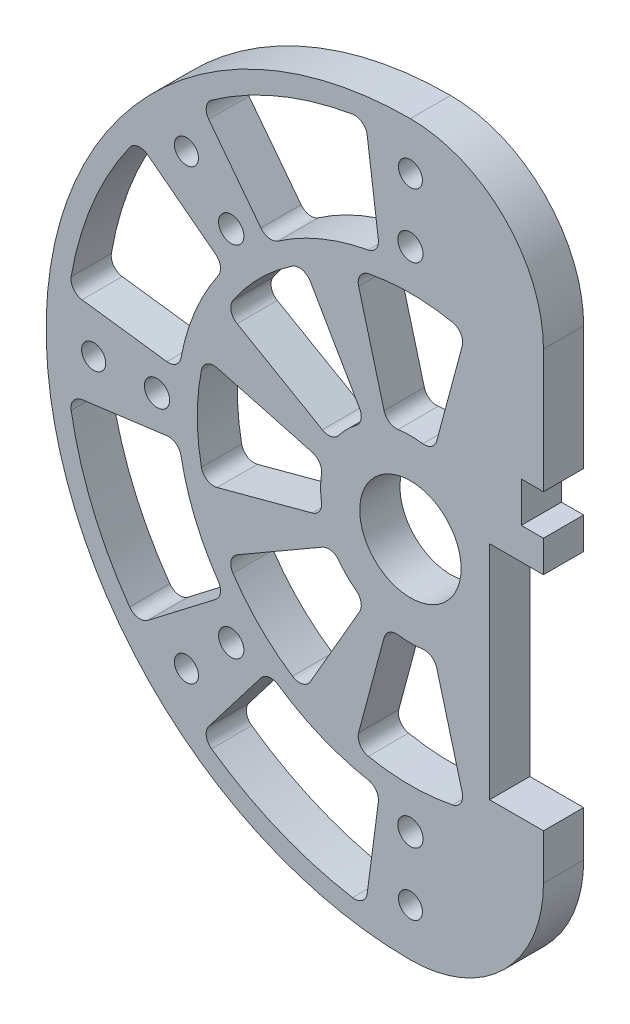
SolidWorks part; units mm, degrees
material "Balsa"
ref_plane "Front Plane" through (0, 0, 0) normal (0, 0, 1) x (1, 0, 0)
ref_plane "Top Plane" through (0, 0, 0) normal (0, 1, 0) x (1, 0, 0)
ref_plane "Right Plane" through (0, 0, 0) normal (1, 0, 0) x (0, 0, -1)
sketch "Sketch1" plane through (0, 0, 0) normal (0, 0, 1) x (1, 0, 0)
  line L0 (45.3154, 21.1309) -> (0, 0) construction
  line L1 (0, 0) -> (35.3553, -35.3553) construction
  line L2 (49.9788, 1.4542) -> (0, 0) construction
  line L3 (0, 0) -> (46.4674, -18.4603) construction
  circle A0 centre (45.3154, 21.1309) radius 1.8986
  circle A1 centre (46.4674, -18.4603) radius 1.9939
  circle A2 centre (0, 0) radius 57.5
  circle A3 centre (0, 0) radius 8
  circle A4 centre (49.9788, 1.4542) radius 1.9939
  circle A5 centre (0, 0) radius 40 construction
  circle A6 centre (0, 0) radius 50 construction
  circle A29 centre (0, -40) radius 1.9939
  circle A30 centre (0, -50) radius 1.8986
  circle A37 centre (-28.2843, -28.2843) radius 1.9939
  circle A38 centre (-35.3553, -35.3553) radius 1.8986
  circle A39 centre (-40, 0) radius 1.9939
  circle A40 centre (-50, 0) radius 1.8986
  circle A41 centre (-28.2843, 28.2843) radius 1.9939
  circle A42 centre (-35.3553, 35.3553) radius 1.8986
  circle A43 centre (0, 40) radius 1.9939
  circle A44 centre (0, 50) radius 1.8986
  circle A45 centre (28.2843, 28.2843) radius 1.9939 construction
  circle A46 centre (35.3553, 35.3553) radius 1.8986 construction
  circle A47 centre (40, 0) radius 1.9939 construction
  circle A48 centre (50, 0) radius 1.8986 construction
  circle A49 centre (28.2843, -28.2843) radius 1.9939 construction
  circle A50 centre (35.3553, -35.3553) radius 1.8986
  dimension "D1" = 115
  dimension "D4" = 3.7973
  dimension "D6" = 100
  dimension "D7" = 80
  dimension "D8" = 3.9878
  dimension "D9" = 3.9878
  dimension "D10" = 23.333
  dimension "D15" = 3.7973
  dimension "D16" = 3.9878
  dimension "D5" = 70
  dimension "D3" = 16
  dimension "D11" = 23.333
  dimension "D21" = 8
extrude "Boss-Extrude1" add sketch "Sketch1" along normal blind 6.35
sketch "Sketch2" plane through (0, 0, 0) normal (0, 0, 1) x (1, 0, 0)
  line L0 (12.5, -29.35) -> (41, -29.35)
  line L1 (41, -29.35) -> (41, 10.65)
  line L2 (41, 10.65) -> (44.5, 10.65)
  line L3 (44.5, 10.65) -> (44.5, 17)
  line L4 (44.5, 17) -> (41, 17)
  line L5 (41, 17) -> (41, 32)
  line L6 (41, 32) -> (21, 32)
  line L7 (21, 32) -> (21, 17)
  line L8 (21, 17) -> (17.5, 17)
  line L9 (17.5, 17) -> (17.5, 10.65)
  line L10 (17.5, 10.65) -> (21, 10.65)
  line L11 (21, 10.65) -> (21, 5.65)
  line L12 (21, 5.65) -> (12.5, 5.65)
  line L13 (12.5, 5.65) -> (12.5, -29.35)
  dimension "D2" = 20
  dimension "D3" = 3.5
  dimension "D4" = 3.5
  dimension "D5" = 15
  dimension "D6" = 21
  dimension "D7" = 6.35
  dimension "D8" = 5
  dimension "D9" = 40
  dimension "D10" = 8.5
  dimension "D11" = 32
extrude "Cut-Extrude1" cut sketch "Sketch2" along normal through all
sketch "Sketch3" plane through (0, 0, 6.35) normal (0, 0, 1) x (1, 0, 0)
  line L0 (41, 32) -> (21, 32) construction
  line L1 (27.825, -8) -> (34.175, -8)
  line L2 (27.825, -8) -> (27.825, 72)
  line L3 (27.825, 72) -> (34.175, 72)
  line L4 (34.175, -8) -> (34.175, 72)
  line L5 (27.825, -8) -> (34.175, 72) construction
  line L6 (27.825, 72) -> (34.175, -8) construction
  point P0 (31, 32)
  dimension "D1" = 6.35
  dimension "D2" = 80
extrude "Cut-Extrude3" cut sketch "Sketch3" against normal through all
sketch "Sketch4" plane through (0, 0, 6.35) normal (0, 0, 1) x (1, 0, 0)
  line L0 (21, -36.5) -> (21, -16.443)
  line L1 (27.825, 32) -> (34.175, 32) construction
  line L2 (21, -16.443) -> (24.175, -16.4703)
  line L3 (24.175, -16.4703) -> (24.175, -57.5)
  line L4 (0, -57.5) -> (24.175, -57.5)
  line L5 (0, 0) -> (98.5911, 0) construction
  line L6 (0, 57.5) -> (24.175, 57.5)
  line L7 (24.175, 16.4703) -> (24.175, 57.5)
  line L8 (21, 16.443) -> (24.175, 16.4703)
  line L9 (21, 36.5) -> (21, 16.443)
  arc A0 (0, -57.5) -> (21, -36.5) centre (0, -36.5) ccw
  arc A1 (0, 57.5) -> (21, 36.5) centre (0, 36.5) cw
  arc A2 (27.825, 50.3192) -> (34.175, 46.242) centre (0, 0) ccw construction
  point P13 (31, 32)
  point P14 (22.5875, -16.4566)
  dimension "D3" = 3.175
  dimension "D4" = 8.4125
extrude "Cut-Extrude4" cut sketch "Sketch4" against normal through all
sketch "Sketch6" plane through (0, 0, 6.35) normal (0, 0, 1) x (1, 0, 0)
  line L0 (-13.692, 3.6688) -> (-32.5034, 8.7093)
  line L1 (-13.692, -3.6688) -> (-32.5034, -8.7093)
  line L2 (0, 0) -> (-74.5627, 0) construction
  arc A0 (-13.692, -3.6688) -> (-13.692, 3.6688) centre (0, 0) cw
  arc A1 (-32.5034, -8.7093) -> (-32.5034, 8.7093) centre (0, 0) cw
  circle A2 centre (0, 0) radius 8 construction
  circle A3 centre (-40, 0) radius 1.9939 construction
  point P8 (-33.65, 0)
  dimension "D1" = 6.175
  dimension "D2" = 6.35
  dimension "D3" = 30
extrude "Cut-Extrude6" cut sketch "Sketch6" against normal through all
fillet "Fillet1" radius 2 4 edges at (-32.5034, -8.7093, 3.175) (-13.692, -3.6688, 3.175) (-13.692, 3.6688, 3.175) (-32.5034, 8.7093, 3.175)
pattern_circular "CirPattern1" count 8 over 360 about axis through (0, 0, 0) along (0, 0, 1) skipping 3, 4, 5 of "Fillet1", "Cut-Extrude6"
sketch "Sketch7" plane through (0, 0, 6.35) normal (0, 0, 1) x (1, 0, 0)
  line L0 (-43.0989, 33.071) -> (-29.2152, 22.4176)
  line L1 (-36.51, 4.8066) -> (-53.8602, 7.0908)
  line L2 (0, 0) -> (-63.1273, 26.1482) construction
  line L3 (0, 0) -> (-71.1611, 0) construction
  arc A0 (-36.51, 4.8066) -> (-29.2152, 22.4176) centre (0, 0) cw
  arc A1 (-43.0989, 33.071) -> (-53.8602, 7.0908) centre (0, 0) ccw
  circle A2 centre (-28.2843, 28.2843) radius 1.9939 construction
  circle A3 centre (-35.3553, 35.3553) radius 1.8987 construction
  circle A4 centre (-28.2843, 28.2843) radius 1.9939 construction
  circle A5 centre (-35.3553, 35.3553) radius 1.8986 construction
  arc A6 (-32.9888, 6.6379) -> (-32.9888, -6.6379) centre (0, 0) ccw construction
  arc A7 (0, 57.5) -> (0, -57.5) centre (0, 0) ccw construction
  point P12 (-34.0219, 14.0923)
  dimension "D3" = 3.175
  dimension "D4" = 3.175
  dimension "D1" = 22.5
  dimension "D2" = 30
extrude "Cut-Extrude7" cut sketch "Sketch7" against normal blind 10
fillet "Fillet2" radius 2 4 edges at (-53.8602, 7.0908, 3.175) (-36.51, 4.8066, 3.175) (-29.2152, 22.4176, 3.175) (-43.0989, 33.071, 3.175)
pattern_circular "CirPattern2" count 8 over 360 about axis through (0, 0, 0) along (0, 0, 1) skipping 2, 3, 4, 5 of "Cut-Extrude7", "Fillet2"
